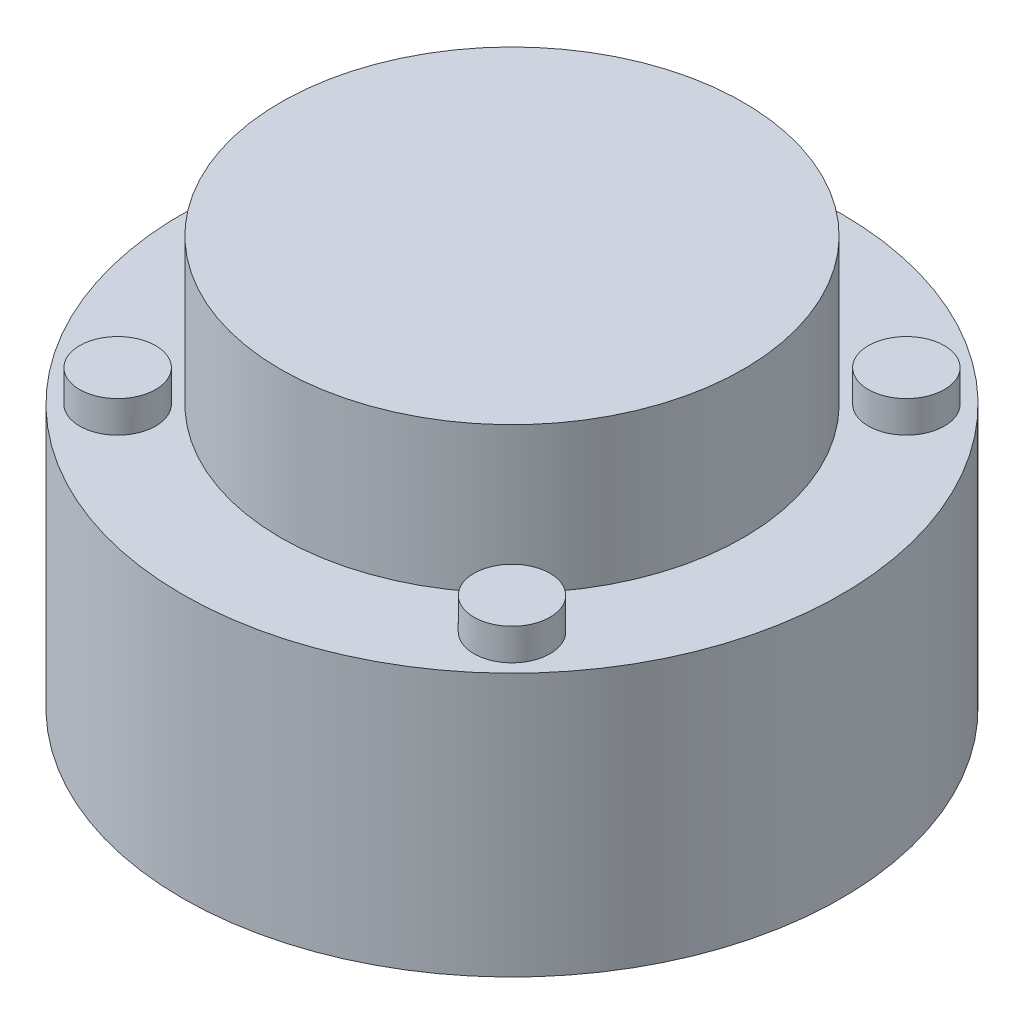
SolidWorks part; units mm, degrees
ref_plane "Front Plane" through (0, 0, 0) normal (0, 0, 1) x (1, 0, 0)
ref_plane "Top Plane" through (0, 0, 0) normal (0, 1, 0) x (1, 0, 0)
ref_plane "Right Plane" through (0, 0, 0) normal (1, 0, 0) x (0, 0, -1)
sketch "Sketch3" plane through (0, 0, 0) normal (0, 0, 1) x (1, 0, 0)
  line L0 (0, 0) -> (26, 0)
  line L1 (26, 0) -> (26, 20.758)
  line L2 (26, 20.758) -> (18.25, 20.758)
  line L3 (18.25, 20.758) -> (18.25, 32.258)
  line L4 (18.25, 32.258) -> (0, 32.258)
  line L5 (0, 32.258) -> (0, 0)
  dimension "D1" = 32.258
  dimension "D2" = 18.25
  dimension "D3" = 26
  dimension "D4" = 11.5
revolve "Revolve1" add sketch "Sketch3" angle 360 about L5
sketch "Sketch4" plane through (0, 20.758, 0) normal (0, 1, 0) x (1, 0, 0)
  line L0 (-15.5563, -15.5563) -> (-15.5563, 15.5563) construction
  line L1 (-15.5563, 15.5563) -> (15.5563, 15.5563) construction
  circle A0 centre (-15.5563, 15.5563) radius 3
  circle A1 centre (15.5563, 15.5563) radius 3
  circle A2 centre (15.5563, -15.5563) radius 3
  circle A3 centre (-15.5563, -15.5563) radius 3
  circle A4 centre (0, 0) radius 22 construction
  dimension "D1" = 6
  dimension "D2" = 44
extrude "Boss-Extrude1" add sketch "Sketch4" along normal blind 2.5
